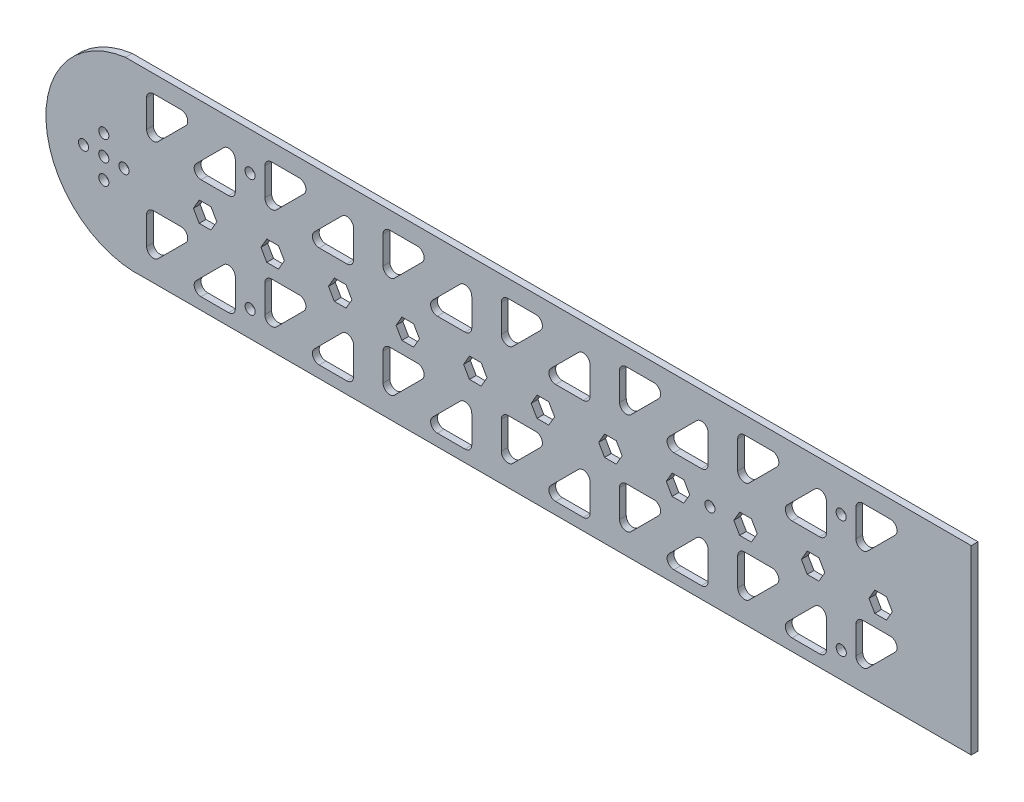
SolidWorks part; units mm, degrees
ref_plane "Ön Düzlem" through (0, 0, 0) normal (0, 0, 1) x (1, 0, 0)
ref_plane "Üst Düzlem" through (0, 0, 0) normal (0, 1, 0) x (1, 0, 0)
ref_plane "Sağ Düzlem" through (0, 0, 0) normal (1, 0, 0) x (0, 0, -1)
sketch "Çizim1" plane through (0, 0, 0) normal (0, 0, 1) x (1, 0, 0)
  line L0 (0, 34.9435) -> (0, -25.0192) construction
  line L1 (-123.6821, 28.6804) -> (123.6821, 28.6804)
  line L3 (-118.1627, -25.0192) -> (118.1627, -25.0192)
  line L5 (-150.2336, 30.0467) -> (150, -30) construction
  line L6 (123.6821, 28.6804) -> (137.2391, 28.6804)
  line L7 (-0.1168, 0.0234) -> (-130.1063, 0.0234) construction
  line L8 (-130.1063, 6.0234) -> (-130.1063, -6.1534) construction
  line L9 (-18.3887, -2.9789) -> (-16.6527, 0.0189)
  line L10 (1.6113, -2.9789) -> (3.3473, 0.0189)
  line L11 (3.3473, 0.0189) -> (1.6191, 3.0211)
  line L12 (1.6191, 3.0211) -> (-1.845, 3.0256)
  line L13 (-1.845, 3.0256) -> (-3.5809, 0.0279)
  line L14 (-3.5809, 0.0279) -> (-1.8528, -2.9744)
  line L15 (-1.8528, -2.9744) -> (1.6113, -2.9789)
  line L16 (-16.6527, 0.0189) -> (-18.3809, 3.0211)
  line L17 (-18.3809, 3.0211) -> (-21.845, 3.0256)
  line L18 (-21.845, 3.0256) -> (-23.5809, 0.0279)
  line L19 (-23.5809, 0.0279) -> (-21.8528, -2.9744)
  line L20 (-21.8528, -2.9744) -> (-18.3887, -2.9789)
  line L21 (-38.3887, -2.9789) -> (-36.6527, 0.0189)
  line L22 (-36.6527, 0.0189) -> (-38.3809, 3.0211)
  line L23 (-38.3809, 3.0211) -> (-41.845, 3.0256)
  line L24 (-41.845, 3.0256) -> (-43.5809, 0.0279)
  line L25 (-43.5809, 0.0279) -> (-41.8528, -2.9744)
  line L26 (-41.8528, -2.9744) -> (-38.3887, -2.9789)
  line L27 (-58.3887, -2.9789) -> (-56.6527, 0.0189)
  line L28 (-56.6527, 0.0189) -> (-58.3809, 3.0211)
  line L29 (-58.3809, 3.0211) -> (-61.845, 3.0256)
  line L30 (-61.845, 3.0256) -> (-63.5809, 0.0279)
  line L31 (-63.5809, 0.0279) -> (-61.8528, -2.9744)
  line L32 (-61.8528, -2.9744) -> (-58.3887, -2.9789)
  line L33 (-78.3887, -2.9789) -> (-76.6527, 0.0189)
  line L34 (-76.6527, 0.0189) -> (-78.3809, 3.0211)
  line L35 (-78.3809, 3.0211) -> (-81.845, 3.0256)
  line L36 (-81.845, 3.0256) -> (-83.5809, 0.0279)
  line L37 (-83.5809, 0.0279) -> (-81.8528, -2.9744)
  line L38 (-81.8528, -2.9744) -> (-78.3887, -2.9789)
  line L39 (-98.3887, -2.9789) -> (-96.6527, 0.0189)
  line L40 (-96.6527, 0.0189) -> (-98.3809, 3.0211)
  line L41 (-98.3809, 3.0211) -> (-101.845, 3.0256)
  line L42 (-101.845, 3.0256) -> (-103.5809, 0.0279)
  line L43 (-103.5809, 0.0279) -> (-101.8528, -2.9744)
  line L44 (-101.8528, -2.9744) -> (-98.3887, -2.9789)
  line L45 (21.6113, -2.9789) -> (23.3473, 0.0189)
  line L46 (18.1472, -2.9744) -> (21.6113, -2.9789)
  line L47 (16.4191, 0.0279) -> (18.1472, -2.9744)
  line L48 (18.155, 3.0256) -> (16.4191, 0.0279)
  line L49 (21.6191, 3.0211) -> (18.155, 3.0256)
  line L50 (23.3473, 0.0189) -> (21.6191, 3.0211)
  line L51 (41.6113, -2.9789) -> (43.3473, 0.0189)
  line L52 (38.1472, -2.9744) -> (41.6113, -2.9789)
  line L53 (36.4191, 0.0279) -> (38.1472, -2.9744)
  line L54 (38.155, 3.0256) -> (36.4191, 0.0279)
  line L55 (41.6191, 3.0211) -> (38.155, 3.0256)
  line L56 (43.3473, 0.0189) -> (41.6191, 3.0211)
  line L57 (61.6113, -2.9789) -> (63.3473, 0.0189)
  line L58 (58.1472, -2.9744) -> (61.6113, -2.9789)
  line L59 (56.4191, 0.0279) -> (58.1472, -2.9744)
  line L60 (58.155, 3.0256) -> (56.4191, 0.0279)
  line L61 (61.6191, 3.0211) -> (58.155, 3.0256)
  line L62 (63.3473, 0.0189) -> (61.6191, 3.0211)
  line L63 (81.6113, -2.9789) -> (83.3473, 0.0189)
  line L64 (78.1472, -2.9744) -> (81.6113, -2.9789)
  line L65 (76.4191, 0.0279) -> (78.1472, -2.9744)
  line L66 (78.155, 3.0256) -> (76.4191, 0.0279)
  line L67 (81.6191, 3.0211) -> (78.155, 3.0256)
  line L68 (83.3473, 0.0189) -> (81.6191, 3.0211)
  line L69 (101.6113, -2.9789) -> (103.3473, 0.0189)
  line L70 (98.1472, -2.9744) -> (101.6113, -2.9789)
  line L71 (96.4191, 0.0279) -> (98.1472, -2.9744)
  line L72 (98.155, 3.0256) -> (96.4191, 0.0279)
  line L73 (101.6191, 3.0211) -> (98.155, 3.0256)
  line L74 (103.3473, 0.0189) -> (101.6191, 3.0211)
  line L75 (-117.433, 15.462) -> (117.433, 15.462) construction
  line L76 (-117.433, 21.4866) -> (-117.433, 13.315)
  line L77 (-115.433, 23.4866) -> (-107.2614, 23.4866)
  line L78 (-105.8472, 20.0724) -> (-114.0187, 11.9008)
  line L79 (-94.5849, 20.0724) -> (-102.7565, 11.9008)
  line L80 (-101.3423, 8.4866) -> (-93.1707, 8.4866)
  line L81 (-91.1707, 10.4866) -> (-91.1707, 18.6582)
  line L82 (-82.433, 21.4866) -> (-82.433, 13.315)
  line L83 (-80.433, 23.4866) -> (-72.2614, 23.4866)
  line L84 (-70.8472, 20.0724) -> (-79.0187, 11.9008)
  line L85 (-59.5849, 20.0724) -> (-67.7565, 11.9008)
  line L86 (-66.3423, 8.4866) -> (-58.1707, 8.4866)
  line L87 (-56.1707, 10.4866) -> (-56.1707, 18.6582)
  line L88 (-47.433, 21.4866) -> (-47.433, 13.315)
  line L89 (-45.433, 23.4866) -> (-37.2614, 23.4866)
  line L90 (-35.8472, 20.0724) -> (-44.0187, 11.9008)
  line L91 (-24.5849, 20.0724) -> (-32.7565, 11.9008)
  line L92 (-31.3423, 8.4866) -> (-23.1707, 8.4866)
  line L93 (-21.1707, 10.4866) -> (-21.1707, 18.6582)
  line L94 (-12.433, 21.4866) -> (-12.433, 13.315)
  line L95 (-10.433, 23.4866) -> (-2.2614, 23.4866)
  line L96 (-0.8472, 20.0724) -> (-9.0187, 11.9008)
  line L97 (10.4151, 20.0724) -> (2.2435, 11.9008)
  line L98 (3.6577, 8.4866) -> (11.8293, 8.4866)
  line L99 (13.8293, 10.4866) -> (13.8293, 18.6582)
  line L100 (22.567, 21.4866) -> (22.567, 13.315)
  line L101 (24.567, 23.4866) -> (32.7386, 23.4866)
  line L102 (34.1528, 20.0724) -> (25.9813, 11.9008)
  line L103 (45.4151, 20.0724) -> (37.2435, 11.9008)
  line L104 (38.6577, 8.4866) -> (46.8293, 8.4866)
  line L105 (48.8293, 10.4866) -> (48.8293, 18.6582)
  line L106 (57.567, 21.4866) -> (57.567, 13.315)
  line L107 (59.567, 23.4866) -> (67.7386, 23.4866)
  line L108 (69.1528, 20.0724) -> (60.9813, 11.9008)
  line L109 (80.4151, 20.0724) -> (72.2435, 11.9008)
  line L110 (73.6577, 8.4866) -> (81.8293, 8.4866)
  line L111 (83.8293, 10.4866) -> (83.8293, 18.6582)
  line L112 (92.567, 21.4866) -> (92.567, 13.315)
  line L113 (94.567, 23.4866) -> (102.7386, 23.4866)
  line L114 (104.1528, 20.0724) -> (95.9813, 11.9008)
  line L118 (-82.433, -8.5134) -> (-82.433, -16.685)
  line L119 (-80.433, -6.5134) -> (-72.2614, -6.5134)
  line L120 (-70.8472, -9.9276) -> (-79.0187, -18.0992)
  line L121 (-59.5849, -9.9276) -> (-67.7565, -18.0992)
  line L122 (-66.3423, -21.5134) -> (-58.1707, -21.5134)
  line L123 (-56.1707, -19.5134) -> (-56.1707, -11.3418)
  line L124 (-47.433, -8.5134) -> (-47.433, -16.685)
  line L125 (-45.433, -6.5134) -> (-37.2614, -6.5134)
  line L126 (-35.8472, -9.9276) -> (-44.0187, -18.0992)
  line L127 (-24.5849, -9.9276) -> (-32.7565, -18.0992)
  line L128 (-31.3423, -21.5134) -> (-23.1707, -21.5134)
  line L129 (-21.1707, -19.5134) -> (-21.1707, -11.3418)
  line L130 (-12.433, -8.5134) -> (-12.433, -16.685)
  line L131 (-10.433, -6.5134) -> (-2.2614, -6.5134)
  line L132 (-0.8472, -9.9276) -> (-9.0187, -18.0992)
  line L133 (10.4151, -9.9276) -> (2.2435, -18.0992)
  line L134 (3.6577, -21.5134) -> (11.8293, -21.5134)
  line L135 (13.8293, -19.5134) -> (13.8293, -11.3418)
  line L136 (22.567, -8.5134) -> (22.567, -16.685)
  line L137 (24.567, -6.5134) -> (32.7386, -6.5134)
  line L138 (34.1528, -9.9276) -> (25.9813, -18.0992)
  line L139 (45.4151, -9.9276) -> (37.2435, -18.0992)
  line L140 (38.6577, -21.5134) -> (46.8293, -21.5134)
  line L141 (48.8293, -19.5134) -> (48.8293, -11.3418)
  line L142 (57.567, -8.5134) -> (57.567, -16.685)
  line L143 (59.567, -6.5134) -> (67.7386, -6.5134)
  line L144 (69.1528, -9.9276) -> (60.9813, -18.0992)
  line L145 (80.4151, -9.9276) -> (72.2435, -18.0992)
  line L146 (73.6577, -21.5134) -> (81.8293, -21.5134)
  line L147 (83.8293, -19.5134) -> (83.8293, -11.3418)
  line L148 (92.567, -8.5134) -> (92.567, -16.685)
  line L149 (94.567, -6.5134) -> (102.7386, -6.5134)
  line L150 (104.1528, -9.9276) -> (95.9813, -18.0992)
  line L154 (-117.433, -8.5134) -> (-117.433, -16.685)
  line L155 (-115.433, -6.5134) -> (-107.2614, -6.5134)
  line L156 (-105.8472, -9.9276) -> (-114.0187, -18.0992)
  line L157 (-94.5849, -9.9276) -> (-102.7565, -18.0992)
  line L158 (-101.3423, -21.5134) -> (-93.1707, -21.5134)
  line L159 (-91.1707, -19.5134) -> (-91.1707, -11.3418)
  line L160 (-0.1168, 0.0234) -> (126.9645, 1.6425) construction
  line L168 (108.6577, 8.4866) -> (116.8293, 8.4866) [skipped]
  line L169 (118.8293, 10.4866) -> (118.8293, 18.6582) [skipped]
  line L170 (118.8293, -19.5134) -> (118.8293, -11.3418) [skipped]
  line L171 (115.4151, -9.9276) -> (107.2435, -18.0992) [skipped]
  line L172 (108.6577, -21.5134) -> (116.8293, -21.5134) [skipped]
  line L173 (115.4151, 20.0724) -> (110.8046, 15.462) [skipped]
  line L176 (110.2391, 21.9008) -> (130.2391, -18.0992) construction
  line L177 (110.2391, -18.0992) -> (130.2391, 21.9008) construction
  line L178 (137.2391, -25.0192) -> (118.1627, -25.0192)
  line L179 (146.7064, 21.9008) -> (126.7064, 21.9008)
  line L180 (146.7468, -18.1182) -> (127.2163, -18.1182)
  line L181 (126.7064, 21.9008) -> (127.2226, -18.6158)
  line L182 (137.2391, 28.6804) -> (144.7064, 28.6804)
  line L183 (146.7064, 26.6804) -> (146.7064, 21.9008)
  line L184 (146.7468, -18.1182) -> (146.7468, -23.0192)
  line L185 (144.7468, -25.0192) -> (137.2391, -25.0192)
  arc A0 (-123.6821, 28.6804) -> (-118.1627, -25.0192) centre (-120.2391, 1.9008) ccw
  arc A1 (124.105, -24.821) -> (118.1627, -25.0192) centre (120.2391, 1.9008) cw
  circle A2 centre (-130.1063, 0.0234) radius 10
  circle A3 centre (-130.1063, 6.0234) radius 1.5
  circle A4 centre (-130.1063, -5.9766) radius 1.5
  circle A5 centre (-136.1063, 0.0234) radius 1.5
  circle A6 centre (-130.1063, 6.0234) radius 1.5
  circle A7 centre (-124.1063, 0.0234) radius 1.5
  circle A8 centre (-130.1063, 0.0234) radius 1.5
  circle A15 centre (-0.1168, 0.0234) radius 3 construction
  arc A16 (-101.3423, 8.4866) -> (-102.7565, 11.9008) centre (-101.3423, 10.4866) cw
  arc A17 (-93.1707, 8.4866) -> (-91.1707, 10.4866) centre (-93.1707, 10.4866) ccw
  arc A18 (-91.1707, 18.6582) -> (-94.5849, 20.0724) centre (-93.1707, 18.6582) ccw
  arc A19 (-114.0187, 11.9008) -> (-117.433, 13.315) centre (-115.433, 13.315) cw
  arc A20 (-107.2614, 23.4866) -> (-105.8472, 20.0724) centre (-107.2614, 21.4866) cw
  arc A21 (-117.433, 21.4866) -> (-115.433, 23.4866) centre (-115.433, 21.4866) cw
  arc A22 (-72.2614, 23.4866) -> (-70.8472, 20.0724) centre (-72.2614, 21.4866) cw
  arc A23 (-82.433, 21.4866) -> (-80.433, 23.4866) centre (-80.433, 21.4866) cw
  arc A24 (-79.0187, 11.9008) -> (-82.433, 13.315) centre (-80.433, 13.315) cw
  arc A25 (-66.3423, 8.4866) -> (-67.7565, 11.9008) centre (-66.3423, 10.4866) cw
  arc A26 (-58.1707, 8.4866) -> (-56.1707, 10.4866) centre (-58.1707, 10.4866) ccw
  arc A27 (-56.1707, 18.6582) -> (-59.5849, 20.0724) centre (-58.1707, 18.6582) ccw
  arc A28 (-37.2614, 23.4866) -> (-35.8472, 20.0724) centre (-37.2614, 21.4866) cw
  arc A29 (-47.433, 21.4866) -> (-45.433, 23.4866) centre (-45.433, 21.4866) cw
  arc A30 (-44.0187, 11.9008) -> (-47.433, 13.315) centre (-45.433, 13.315) cw
  arc A31 (-31.3423, 8.4866) -> (-32.7565, 11.9008) centre (-31.3423, 10.4866) cw
  arc A32 (-23.1707, 8.4866) -> (-21.1707, 10.4866) centre (-23.1707, 10.4866) ccw
  arc A33 (-21.1707, 18.6582) -> (-24.5849, 20.0724) centre (-23.1707, 18.6582) ccw
  arc A34 (-2.2614, 23.4866) -> (-0.8472, 20.0724) centre (-2.2614, 21.4866) cw
  arc A35 (-12.433, 21.4866) -> (-10.433, 23.4866) centre (-10.433, 21.4866) cw
  arc A36 (-9.0187, 11.9008) -> (-12.433, 13.315) centre (-10.433, 13.315) cw
  arc A37 (3.6577, 8.4866) -> (2.2435, 11.9008) centre (3.6577, 10.4866) cw
  arc A38 (11.8293, 8.4866) -> (13.8293, 10.4866) centre (11.8293, 10.4866) ccw
  arc A39 (13.8293, 18.6582) -> (10.4151, 20.0724) centre (11.8293, 18.6582) ccw
  arc A40 (32.7386, 23.4866) -> (34.1528, 20.0724) centre (32.7386, 21.4866) cw
  arc A41 (22.567, 21.4866) -> (24.567, 23.4866) centre (24.567, 21.4866) cw
  arc A42 (25.9813, 11.9008) -> (22.567, 13.315) centre (24.567, 13.315) cw
  arc A43 (38.6577, 8.4866) -> (37.2435, 11.9008) centre (38.6577, 10.4866) cw
  arc A44 (46.8293, 8.4866) -> (48.8293, 10.4866) centre (46.8293, 10.4866) ccw
  arc A45 (48.8293, 18.6582) -> (45.4151, 20.0724) centre (46.8293, 18.6582) ccw
  arc A46 (67.7386, 23.4866) -> (69.1528, 20.0724) centre (67.7386, 21.4866) cw
  arc A47 (57.567, 21.4866) -> (59.567, 23.4866) centre (59.567, 21.4866) cw
  arc A48 (60.9813, 11.9008) -> (57.567, 13.315) centre (59.567, 13.315) cw
  arc A49 (73.6577, 8.4866) -> (72.2435, 11.9008) centre (73.6577, 10.4866) cw
  arc A50 (81.8293, 8.4866) -> (83.8293, 10.4866) centre (81.8293, 10.4866) ccw
  arc A51 (83.8293, 18.6582) -> (80.4151, 20.0724) centre (81.8293, 18.6582) ccw
  arc A52 (102.7386, 23.4866) -> (104.1528, 20.0724) centre (102.7386, 21.4866) cw
  arc A53 (92.567, 21.4866) -> (94.567, 23.4866) centre (94.567, 21.4866) cw
  arc A54 (95.9813, 11.9008) -> (92.567, 13.315) centre (94.567, 13.315) cw
  arc A58 (-72.2614, -6.5134) -> (-70.8472, -9.9276) centre (-72.2614, -8.5134) cw
  arc A59 (-82.433, -8.5134) -> (-80.433, -6.5134) centre (-80.433, -8.5134) cw
  arc A60 (-79.0187, -18.0992) -> (-82.433, -16.685) centre (-80.433, -16.685) cw
  arc A61 (-66.3423, -21.5134) -> (-67.7565, -18.0992) centre (-66.3423, -19.5134) cw
  arc A62 (-58.1707, -21.5134) -> (-56.1707, -19.5134) centre (-58.1707, -19.5134) ccw
  arc A63 (-56.1707, -11.3418) -> (-59.5849, -9.9276) centre (-58.1707, -11.3418) ccw
  arc A64 (-37.2614, -6.5134) -> (-35.8472, -9.9276) centre (-37.2614, -8.5134) cw
  arc A65 (-47.433, -8.5134) -> (-45.433, -6.5134) centre (-45.433, -8.5134) cw
  arc A66 (-44.0187, -18.0992) -> (-47.433, -16.685) centre (-45.433, -16.685) cw
  arc A67 (-31.3423, -21.5134) -> (-32.7565, -18.0992) centre (-31.3423, -19.5134) cw
  arc A68 (-23.1707, -21.5134) -> (-21.1707, -19.5134) centre (-23.1707, -19.5134) ccw
  arc A69 (-21.1707, -11.3418) -> (-24.5849, -9.9276) centre (-23.1707, -11.3418) ccw
  arc A70 (-2.2614, -6.5134) -> (-0.8472, -9.9276) centre (-2.2614, -8.5134) cw
  arc A71 (-12.433, -8.5134) -> (-10.433, -6.5134) centre (-10.433, -8.5134) cw
  arc A72 (-9.0187, -18.0992) -> (-12.433, -16.685) centre (-10.433, -16.685) cw
  arc A73 (3.6577, -21.5134) -> (2.2435, -18.0992) centre (3.6577, -19.5134) cw
  arc A74 (11.8293, -21.5134) -> (13.8293, -19.5134) centre (11.8293, -19.5134) ccw
  arc A75 (13.8293, -11.3418) -> (10.4151, -9.9276) centre (11.8293, -11.3418) ccw
  arc A76 (32.7386, -6.5134) -> (34.1528, -9.9276) centre (32.7386, -8.5134) cw
  arc A77 (22.567, -8.5134) -> (24.567, -6.5134) centre (24.567, -8.5134) cw
  arc A78 (25.9813, -18.0992) -> (22.567, -16.685) centre (24.567, -16.685) cw
  arc A79 (38.6577, -21.5134) -> (37.2435, -18.0992) centre (38.6577, -19.5134) cw
  arc A80 (46.8293, -21.5134) -> (48.8293, -19.5134) centre (46.8293, -19.5134) ccw
  arc A81 (48.8293, -11.3418) -> (45.4151, -9.9276) centre (46.8293, -11.3418) ccw
  arc A82 (67.7386, -6.5134) -> (69.1528, -9.9276) centre (67.7386, -8.5134) cw
  arc A83 (57.567, -8.5134) -> (59.567, -6.5134) centre (59.567, -8.5134) cw
  arc A84 (60.9813, -18.0992) -> (57.567, -16.685) centre (59.567, -16.685) cw
  arc A85 (73.6577, -21.5134) -> (72.2435, -18.0992) centre (73.6577, -19.5134) cw
  arc A86 (81.8293, -21.5134) -> (83.8293, -19.5134) centre (81.8293, -19.5134) ccw
  arc A87 (83.8293, -11.3418) -> (80.4151, -9.9276) centre (81.8293, -11.3418) ccw
  arc A88 (102.7386, -6.5134) -> (104.1528, -9.9276) centre (102.7386, -8.5134) cw
  arc A89 (92.567, -8.5134) -> (94.567, -6.5134) centre (94.567, -8.5134) cw
  arc A90 (95.9813, -18.0992) -> (92.567, -16.685) centre (94.567, -16.685) cw
  arc A94 (-107.2614, -6.5134) -> (-105.8472, -9.9276) centre (-107.2614, -8.5134) cw
  arc A95 (-117.433, -8.5134) -> (-115.433, -6.5134) centre (-115.433, -8.5134) cw
  arc A96 (-114.0187, -18.0992) -> (-117.433, -16.685) centre (-115.433, -16.685) cw
  arc A97 (-101.3423, -21.5134) -> (-102.7565, -18.0992) centre (-101.3423, -19.5134) cw
  arc A98 (-93.1707, -21.5134) -> (-91.1707, -19.5134) centre (-93.1707, -19.5134) ccw
  arc A99 (-91.1707, -11.3418) -> (-94.5849, -9.9276) centre (-93.1707, -11.3418) ccw
  arc A100 (116.8293, 8.4866) -> (118.8293, 10.4866) centre (116.8293, 10.4866) ccw [skipped]
  arc A101 (108.6577, 8.4866) -> (107.2435, 11.9008) centre (108.6577, 10.4866) cw [skipped]
  arc A102 (118.8293, -11.3418) -> (115.4151, -9.9276) centre (116.8293, -11.3418) ccw [skipped]
  arc A103 (108.6577, -21.5134) -> (107.2435, -18.0992) centre (108.6577, -19.5134) cw [skipped]
  arc A104 (118.8293, 18.6582) -> (115.4151, 20.0724) centre (116.8293, 18.6582) ccw [skipped]
  arc A105 (116.8293, -21.5134) -> (118.8293, -19.5134) centre (116.8293, -19.5134) ccw [skipped]
  arc A108 (144.7468, -25.0192) -> (146.7468, -23.0192) centre (144.7468, -23.0192) ccw
  arc A109 (144.7064, 28.6804) -> (146.7064, 26.6804) centre (144.7064, 26.6804) cw
  circle A110 centre (131.8598, 25.9008) radius 1.5
  circle A111 centre (141.8598, 25.9008) radius 1.5
  circle A112 centre (131.8598, -22.0992) radius 1.5
  circle A113 centre (141.8598, -22.0992) radius 1.5
  point P0 (0, 0)
  point P23 (120.3522, -2.2451)
  point P31 (-130.1063, 0.0234)
  point P124 (-117.433, 8.4866)
  point P127 (-102.433, 23.4866)
  point P130 (-117.433, 23.4866)
  dimension "D1" = 20
  dimension "D3" = 3
  dimension "D6" = 6
  dimension "D10" = 2
  dimension "D16" = 2
  dimension "D4" = 6
  dimension "D8" = 15
  dimension "D9" = 15
  dimension "D13" = 40
  dimension "D14" = 20
  dimension "D15" = 20
  dimension "D7" = 6
  dimension "D11" = 7
  dimension "D12" = 2
  dimension "D5" = 4
extrude "Yükseklik-Ekstrüzyon2" add sketch "Çizim1" along normal blind 2
sketch "Çizim9" plane through (0, 0, 0) normal (0, 0, -1) x (-1, 0, 0)
  line L0 (-92.567, 17.4008) -> (-83.8293, 17.4008) construction
  line L1 (-92.567, 21.4866) -> (-92.567, 13.315) construction
  line L2 (-83.8293, 10.4866) -> (-83.8293, 18.6582) construction
  line L3 (-88.1982, 17.4008) -> (-88.1982, -25.6798) construction
  line L4 (-96.4191, 0.0279) -> (-83.3473, 0.0189) construction
  line L5 (-1.8099, 9.7212) -> (-1.8099, -20.2788) construction
  line L6 (-96.4191, 0.0279) -> (96.6527, 0.0189) construction
  circle A0 centre (-88.1982, 17.4008) radius 1.5
  circle A1 centre (-88.2222, -17.3564) radius 1.5
  arc A2 (-3.6577, 8.4866) -> (-2.2435, 11.9008) centre (-3.6577, 10.4866) ccw construction
  arc A3 (-3.6577, -21.5134) -> (-2.2435, -18.0992) centre (-3.6577, -19.5134) ccw construction
  circle A4 centre (86.8018, 17.4008) radius 1.5
  circle A5 centre (86.7778, -17.3564) radius 1.5
  dimension "D1" = 2
extrude "Kes-Ekstrüzyon5" cut sketch "Çizim9" against normal blind 10
sketch "Çizim10" plane through (0, 0, 2) normal (0, 0, 1) x (1, 0, 0)
  circle A0 centre (49.3473, 0) radius 1.5
  dimension "D1" = 3
  dimension "D2" = 6
extrude "Kes-Ekstrüzyon7" cut sketch "Çizim10" against normal blind 10
sketch "Çizim11" plane through (0, 0, 2) normal (0, 0, 1) x (1, 0, 0)
  line L0 (-123.6821, 28.6804) -> (144.7064, 28.6804) construction
  line L1 (126.7064, 28.6804) -> (149.6239, 28.6804)
  line L2 (126.7064, 28.6804) -> (126.7064, -25.0192)
  line L3 (126.7064, -25.0192) -> (149.6239, -25.0192)
  line L4 (149.6239, 28.6804) -> (149.6239, -25.0192)
extrude "Kes-Ekstrüzyon8" cut sketch "Çizim11" against normal blind 10
sketch "Çizim12" plane through (0, 0, 2) normal (0, 0, 1) x (1, 0, 0)
  line L0 (-123.6821, 28.6804) -> (126.7064, 28.6804) construction
  line L1 (124.7064, 28.6804) -> (126.7064, 28.6804)
  line L2 (124.7064, 28.6804) -> (124.7064, -25.0192)
  line L3 (124.7064, -25.0192) -> (126.7064, -25.0192)
  line L4 (126.7064, 28.6804) -> (126.7064, -25.0192)
  dimension "D1" = 2
extrude "Yükseklik-Ekstrüzyon3" add sketch "Çizim12" along normal blind 20
sketch "Çizim13" plane through (126.7064, 0, 0) normal (1, 0, 0) x (0, 0, -1)
  line L0 (-2, 0.0184) -> (0, 0.0189) construction
  line L1 (-22, -25.0192) -> (-22, 28.6804) construction
  line L2 (0, 28.6804) -> (0, -25.0192) construction
  line L4 (-22, 2.408) -> (-22, -17.592)
  line L5 (-22, -17.592) -> (-2, -17.592)
  line L6 (-2, 2.408) -> (-2, -17.592)
  line L8 (-22, 2.408) -> (-22, 22.408)
  line L9 (-22, 22.408) -> (-2, 22.408)
  line L10 (-2, 2.408) -> (-2, 22.408)
  line L11 (0, -25.0192) -> (-22, -25.0192) construction
  dimension "D1" = 20
  dimension "D2" = 20
  dimension "D3" = 2
  dimension "8" = 7.4272
extrude "Kes-Ekstrüzyon10" cut sketch "Çizim13" against normal blind 20
sketch "Çizim14" plane through (124.7064, 0, 0) normal (-1, 0, 0) x (0, 0, 1)
  line L1 (2, 28.6804) -> (22, 28.6804)
  line L2 (2, 28.6804) -> (2, -25.0192)
  line L3 (2, -25.0192) -> (22, -25.0192)
  line L4 (22, 28.6804) -> (22, -25.0192)
extrude "Kes-Ekstrüzyon11" cut sketch "Çizim14" against normal blind 10
